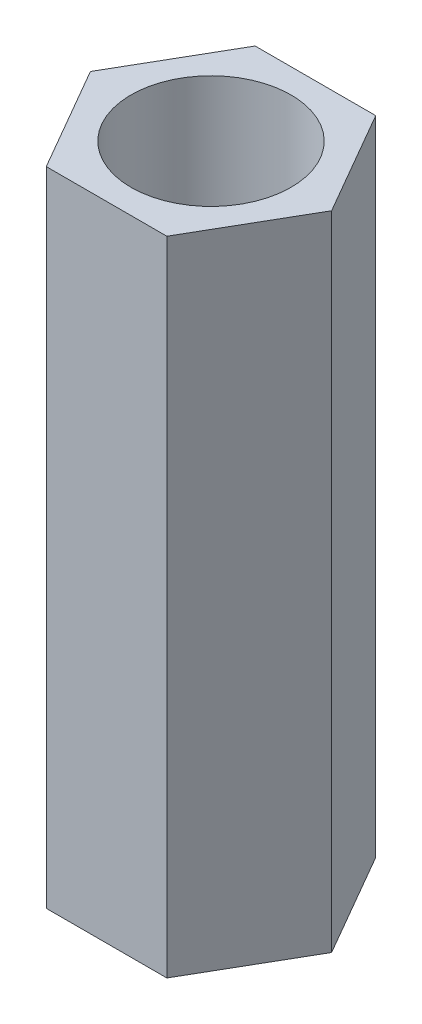
SolidWorks part; units mm, degrees
ref_plane "Front Plane" through (0, 0, 0) normal (0, 0, 1) x (1, 0, 0)
ref_plane "Top Plane" through (0, 0, 0) normal (0, 1, 0) x (1, 0, 0)
ref_plane "Right Plane" through (0, 0, 0) normal (1, 0, 0) x (0, 0, -1)
sketch "Sketch1" plane through (0, 0, 0) normal (0, 1, 0) x (1, 0, 0)
  line L1 (0.979, -1.6957) -> (1.958, 0)
  line L2 (1.958, 0) -> (0.979, 1.6957)
  line L3 (0.979, 1.6957) -> (-0.979, 1.6957)
  line L4 (-0.979, 1.6957) -> (-1.958, 0)
  line L5 (-1.958, 0) -> (-0.979, -1.6957)
  line L6 (-0.979, -1.6957) -> (0.979, -1.6957)
  circle A0 centre (0, 0) radius 1.6957 construction
  circle A1 centre (0, 0) radius 1.3
  dimension "D1" = 2.6
extrude "Boss-Extrude1" add sketch "Sketch1" along normal blind 10.43
